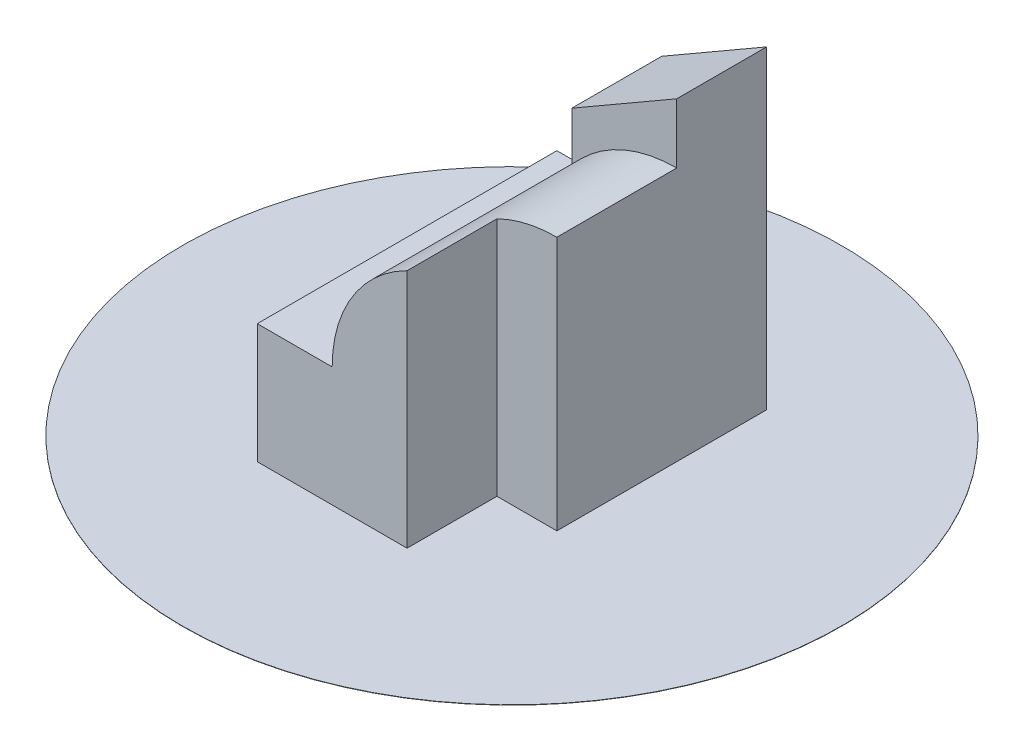
SolidWorks part; units mm, degrees
ref_plane "Front Plane" through (0, 0, 0) normal (0, 0, 1) x (1, 0, 0)
ref_plane "Top Plane" through (0, 0, 0) normal (0, 1, 0) x (1, 0, 0)
ref_plane "Right Plane" through (0, 0, 0) normal (1, 0, 0) x (0, 0, -1)
sketch "Sketch1" plane through (0, 0, 0) normal (0, 0, 1) x (1, 0, 0)
  line L0 (0, 0) -> (70, 0)
  line L1 (70, 0) -> (70, 85)
  line L3 (0, 40) -> (0, 0)
  line L4 (25, 40) -> (0, 40)
  arc A0 (70, 85) -> (25, 40) centre (70, 40) ccw
  dimension "D1" = 45
  dimension "D2" = 40
  dimension "D3" = 40
  dimension "D4" = 70
extrude "Extrude1" add sketch "Sketch1" against normal blind 100
sketch "Sketch2" plane through (0, 0, 0) normal (0, 1, 0) x (1, 0, 0)
  line L1 (70, 100) -> (35, 100)
  line L2 (70, 100) -> (70, 70)
  line L3 (70, 70) -> (35, 70)
  line L4 (35, 100) -> (35, 70)
  dimension "D1" = 30
  dimension "D2" = 35
extrude "Extrude2" add sketch "Sketch2" along normal blind 105
sketch "Sketch3" plane through (0, 0, 0) normal (0, 1, 0) x (1, 0, 0)
  line L1 (70, 0) -> (50, 0)
  line L2 (70, 0) -> (70, 30)
  line L3 (70, 30) -> (50, 30)
  line L4 (50, 0) -> (50, 30)
  dimension "D1" = 20
  dimension "D2" = 30
extrude "Extrude3" cut sketch "Sketch3" along normal blind 105
sketch "Sketch4" plane through (0, 0, -70) normal (0, 0, 1) x (1, 0, 0)
  line L0 (70, 105) -> (35, 105)
  line L1 (35, 105) -> (35, 84.7927)
  line L2 (35, 105) -> (35, 68.2843) construction
  line L3 (35, 84.7927) -> (70, 105)
  dimension "D1" = 30
extrude "Extrude4" cut sketch "Sketch4" against normal through all
sketch "Sketch5" plane through (0, 0, 0) normal (0, 1, 0) x (1, 0, 0)
  line L0 (70, 100) -> (0, 0) construction
  circle A0 centre (35, 50) radius 110
  dimension "D1" = 220
extrude "Extrude5" add sketch "Sketch5" along normal blind 0.1
